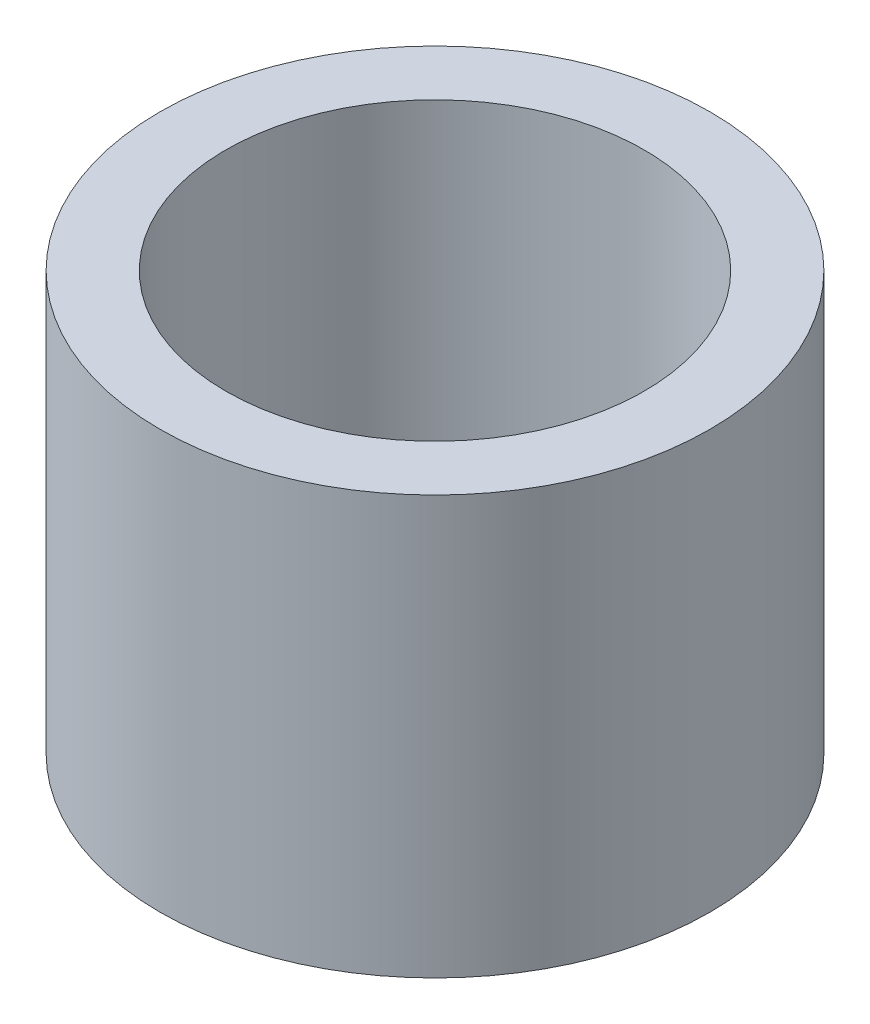
SolidWorks part; units mm, degrees
material "PVC 0.007 Plasticized"
ref_plane "Front Plane" through (0, 0, 0) normal (0, 0, 1) x (1, 0, 0)
ref_plane "Top Plane" through (0, 0, 0) normal (0, 1, 0) x (1, 0, 0)
ref_plane "Right Plane" through (0, 0, 0) normal (1, 0, 0) x (0, 0, -1)
sketch "Sketch1" plane through (0, 0, 0) normal (0, 1, 0) x (1, 0, 0)
  circle A0 centre (0, 0) radius 12.7
  circle A1 centre (0, 0) radius 16.7005
  dimension "D1" = 25.4
  dimension "D2" = 33.401
extrude "Boss-Extrude1" add sketch "Sketch1" along normal up to surface (25.4 mm away)
